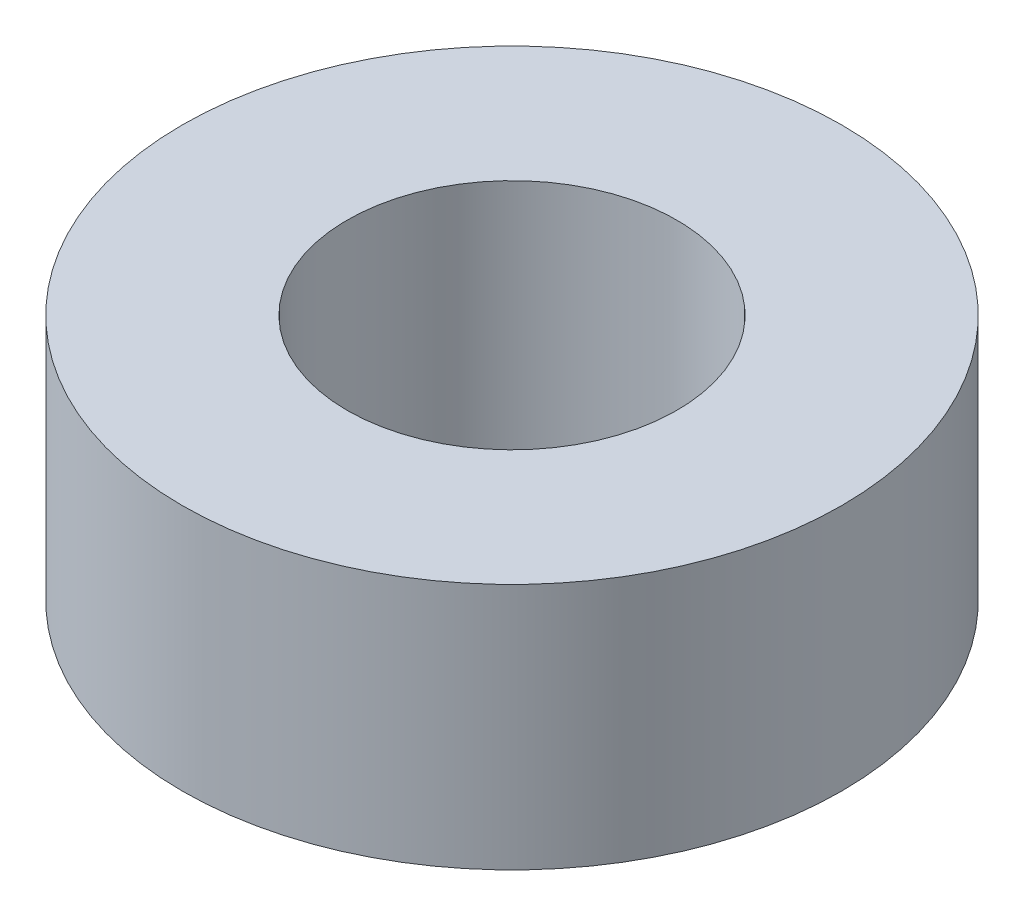
SolidWorks part; units mm, degrees
material "不锈钢 (铁素体)"
ref_plane "前视基准面" through (0, 0, 0) normal (0, 0, 1) x (1, 0, 0)
ref_plane "上视基准面" through (0, 0, 0) normal (0, 1, 0) x (1, 0, 0)
ref_plane "右视基准面" through (0, 0, 0) normal (1, 0, 0) x (0, 0, -1)
sketch "草图1" plane through (0, 0, 0) normal (0, 1, 0) x (1, 0, 0)
  circle A0 centre (0, 0) radius 2
  circle A1 centre (0, 0) radius 4
  dimension "D1" = 8
  dimension "D2" = 4
extrude "凸台-拉伸1" add sketch "草图1" along normal blind 3
